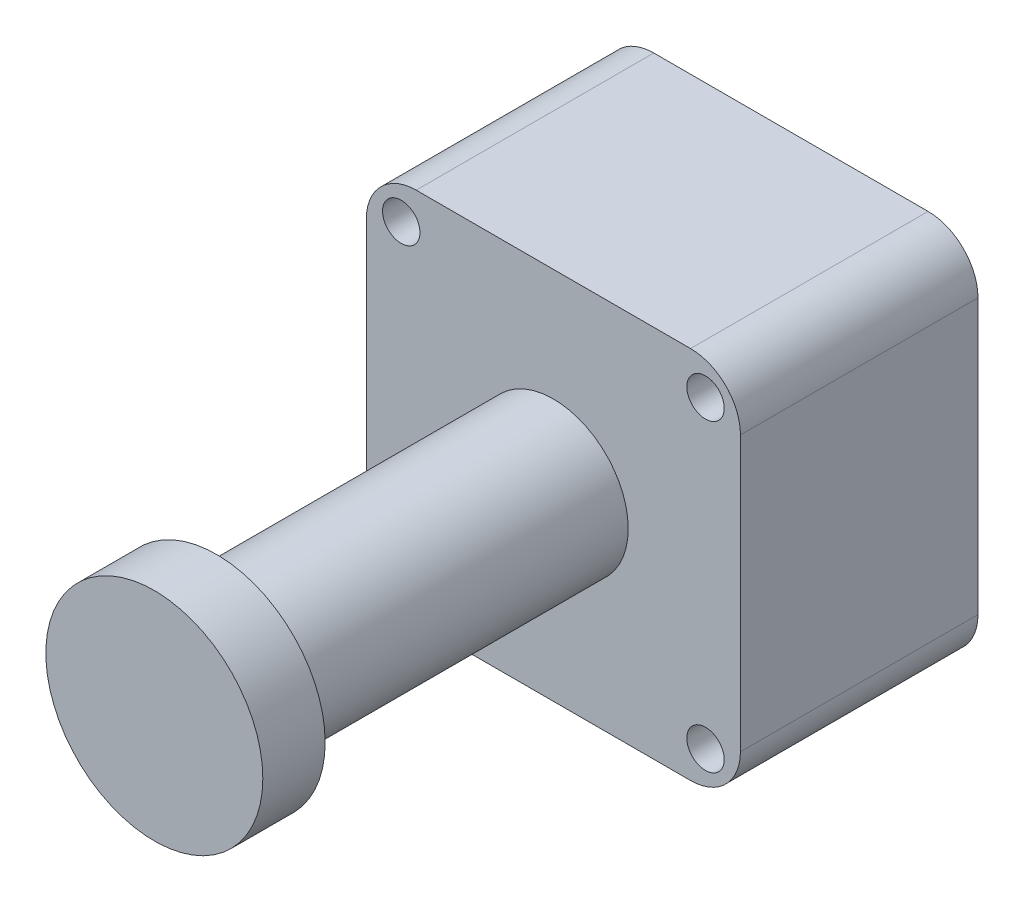
SolidWorks part; units mm, degrees
material "ABS"
ref_plane "Front Plane" through (0, 0, 0) normal (0, 0, 1) x (1, 0, 0)
ref_plane "Top Plane" through (0, 0, 0) normal (0, 1, 0) x (1, 0, 0)
ref_plane "Right Plane" through (0, 0, 0) normal (1, 0, 0) x (0, 0, -1)
sketch "Sketch1" plane through (0, 0, 0) normal (0, 0, 1) x (1, 0, 0)
  line L1 (-15, -15) -> (15, -15)
  line L2 (-15, -15) -> (-15, 15)
  line L3 (-15, 15) -> (15, 15)
  line L4 (15, -15) -> (15, 15)
  line L5 (-15, -15) -> (15, 15) construction
  line L6 (-15, 15) -> (15, -15) construction
  point P0 (0, 0)
  dimension "D1" = 30
extrude "Boss-Extrude1" add sketch "Sketch1" along normal blind 19.05
fillet "Fillet1" radius 4 4 edges at (15, -15, 9.525) (-15, -15, 9.525) (-15, 15, 9.525) (15, 15, 9.525)
sketch "Sketch2" plane through (0, 0, 19.05) normal (0, 0, 1) x (1, 0, 0)
  line L1 (-12.2, -12.2) -> (12.2, -12.2) construction
  line L2 (-12.2, -12.2) -> (-12.2, 12.2) construction
  line L3 (-12.2, 12.2) -> (12.2, 12.2) construction
  line L4 (12.2, -12.2) -> (12.2, 12.2) construction
  line L5 (-12.2, -12.2) -> (12.2, 12.2) construction
  line L6 (-12.2, 12.2) -> (12.2, -12.2) construction
  circle A0 centre (-12.2, 12.2) radius 1.5
  circle A1 centre (12.2, 12.2) radius 1.5
  circle A2 centre (12.2, -12.2) radius 1.5
  circle A3 centre (-12.2, -12.2) radius 1.5
  point P0 (0, 0)
  dimension "D1" = 3
  dimension "D2" = 24.4
extrude "Cut-Extrude1" cut sketch "Sketch2" against normal through all
sketch "Sketch3" plane through (0, 0, 19.05) normal (0, 0, 1) x (1, 0, 0)
  circle A0 centre (0, 0) radius 8.7
  dimension "D1" = 17.4
extrude "Boss-Extrude2" add sketch "Sketch3" along normal blind 32
sketch "Sketch4" plane through (0, 0, 19.05) normal (0, 0, 1) x (1, 0, 0)
  circle A0 centre (0, 0) radius 6
  circle A1 centre (0, 0) radius 8.7 construction
  circle A2 centre (0, 0) radius 8.7
  dimension "D1" = 12
extrude "Cut-Extrude2" cut sketch "Sketch4" along normal blind 27
